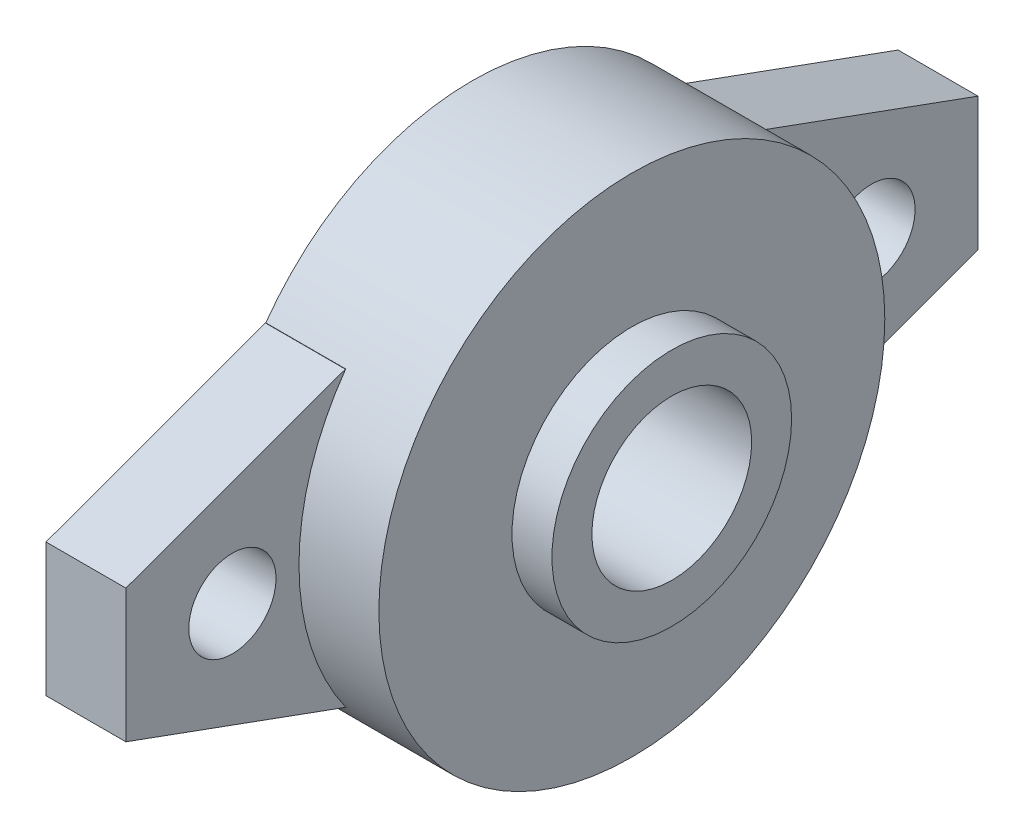
SolidWorks part; units mm, degrees
ref_plane "Front" through (0, 0, 0) normal (0, 0, 1) x (1, 0, 0)
ref_plane "Top" through (0, 0, 0) normal (0, 1, 0) x (1, 0, 0)
ref_plane "Right" through (0, 0, 0) normal (1, 0, 0) x (0, 0, -1)
other "Configuration Table"
sketch "Sketch1" plane through (0, 0, 0) normal (1, 0, 0) x (0, 0, -1)
  circle A0 centre (0, 0) radius 19
  circle A1 centre (0, 0) radius 6
  dimension "D1" = 38
extrude "Boss-Extrude1" add sketch "Sketch1" along normal blind 12
sketch "Sketch2" plane through (12, 0, 0) normal (1, 0, 0) x (0, 0, -1)
  circle A0 centre (0, 0) radius 6
  circle A1 centre (0, 0) radius 9
extrude "Boss-Extrude2" add sketch "Sketch2" along normal blind 3
sketch "Sketch3" plane through (0, 0, 0) normal (-1, 0, 0) x (0, 0, 1)
  line L1 (32, -11) -> (-32, -11)
  line L2 (32, -11) -> (32, 11)
  line L3 (32, 11) -> (-32, 11)
  line L4 (-32, -11) -> (-32, 11)
  point P7 (-26.042, 7.802)
  dimension "D1" = 64
  dimension "D2" = 22
  dimension "D3" = 11
  dimension "D4" = 32
extrude "Boss-Extrude3" add sketch "Sketch3" against normal blind 6
chamfer "Chamfer1" distance 6 angle 70 4 edges at (3, -11, 32) (3, -11, -32) (3, 11, 32) (3, 11, -32)
sketch "Sketch4" plane through (0, 0, 0) normal (-1, 0, 0) x (0, 0, 1)
  line L0 (-32, 5) -> (-32, -5) construction
  circle A0 centre (-24, 0) radius 3.2759
  point P2 (0, 0)
  dimension "D1" = 8
extrude "Cut-Extrude1" cut sketch "Sketch4" against normal blind 6
pattern_linear "LPattern1" count 2 spacing 48 along (0, 0, 1) of "Cut-Extrude1"
sketch "Sketch5" plane through (0, 0, 0) normal (-1, 0, 0) x (0, 0, 1)
  circle A0 centre (0, 0) radius 6
extrude "Cut-Extrude2" cut sketch "Sketch5" against normal blind 6
